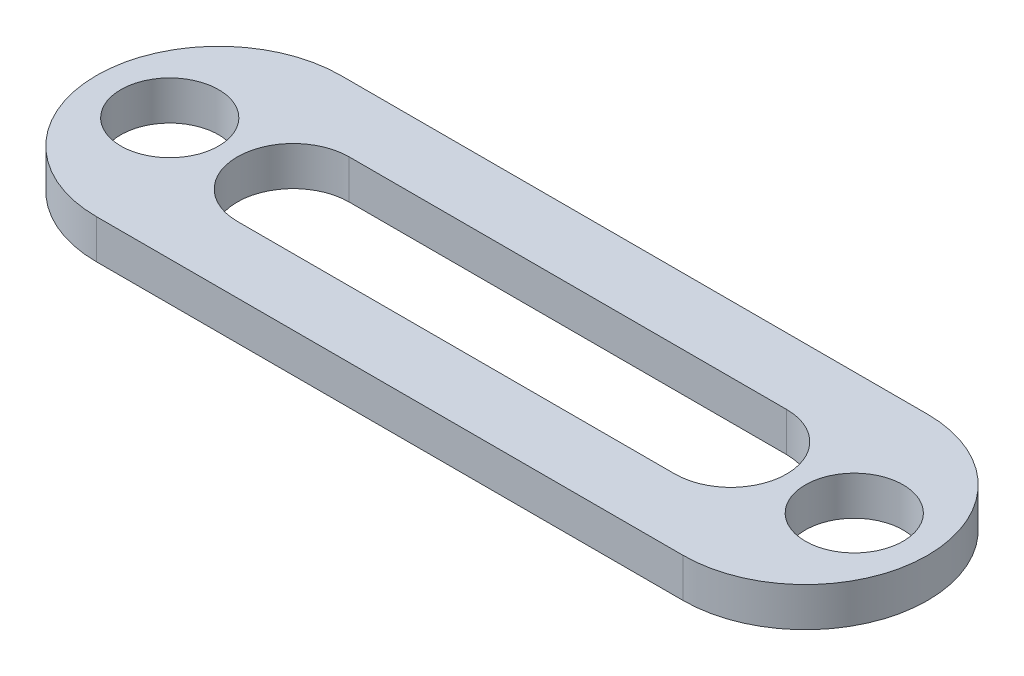
SolidWorks part; units mm, degrees
ref_plane "Front Plane" through (0, 0, 0) normal (0, 0, 1) x (1, 0, 0)
ref_plane "Top Plane" through (0, 0, 0) normal (0, 1, 0) x (1, 0, 0)
ref_plane "Right Plane" through (0, 0, 0) normal (1, 0, 0) x (0, 0, -1)
sketch "Sketch1" plane through (0, 0, 0) normal (0, 1, 0) x (1, 0, 0)
  line L0 (0, 0) -> (15.24, 0) construction
  line L1 (0, 3.175) -> (15.24, 3.175)
  line L2 (0, -3.175) -> (15.24, -3.175)
  line L3 (-1.27, 0) -> (-3.175, 0) construction
  line L4 (16.51, 0) -> (18.415, 0) construction
  line L5 (1.9372, 0) -> (13.3028, 0) construction
  line L6 (1.9372, 1.4517) -> (13.3028, 1.4517)
  line L7 (1.9372, -1.4517) -> (13.3028, -1.4517)
  arc A0 (0, 3.175) -> (0, -3.175) centre (0, 0) ccw
  arc A1 (15.24, -3.175) -> (15.24, 3.175) centre (15.24, 0) ccw
  circle A2 centre (-1.27, 0) radius 1.27
  circle A3 centre (16.51, 0) radius 1.27
  arc A4 (1.9372, 1.4517) -> (1.9372, -1.4517) centre (1.9372, 0) ccw
  arc A5 (13.3028, -1.4517) -> (13.3028, 1.4517) centre (13.3028, 0) ccw
  point P3 (7.62, 0)
  point P16 (7.62, 0)
  dimension "D2" = 6.35
  dimension "D3" = 2.54
  dimension "D4" = 2.54
  dimension "D1" = 15.24
  dimension "D5" = 17.78
extrude "Boss-Extrude4" add sketch "Sketch1" along normal blind 1.016
